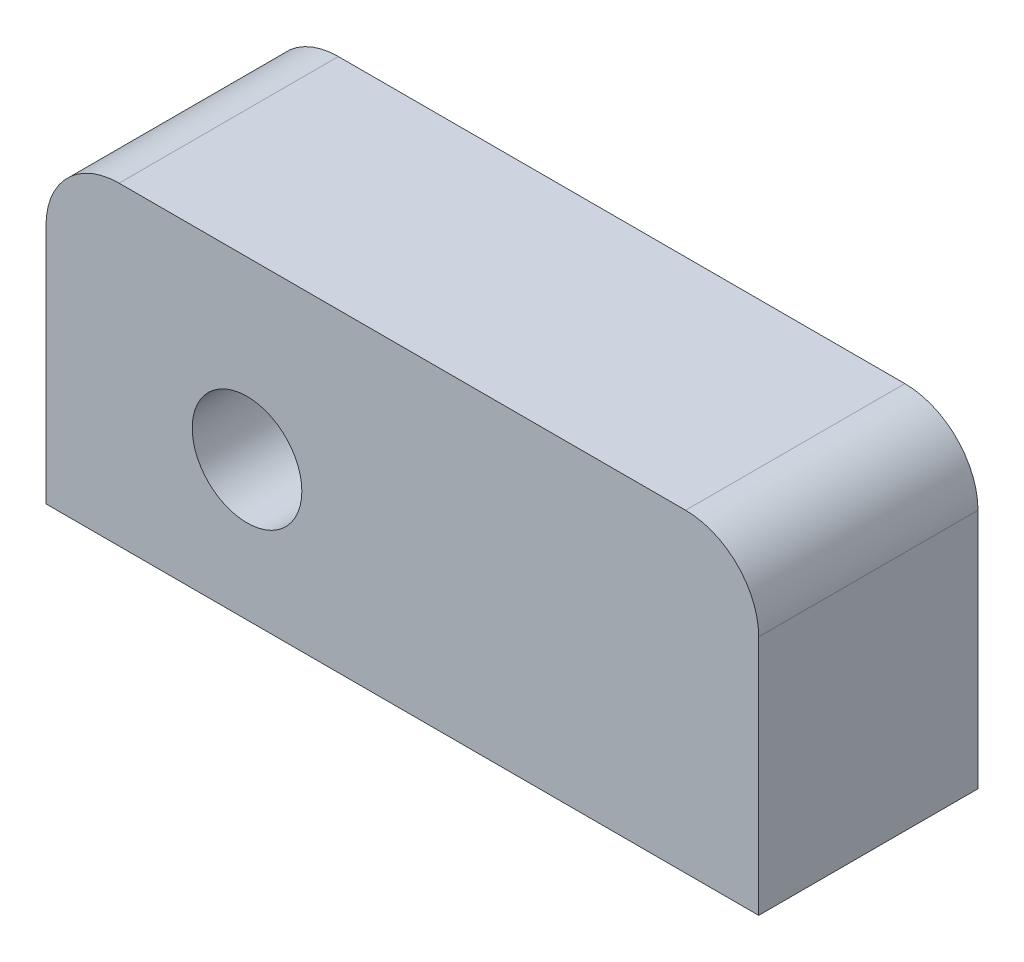
SolidWorks part; units mm, degrees
ref_plane "Płaszczyzna przednia" through (0, 0, 0) normal (0, 0, 1) x (1, 0, 0)
ref_plane "Płaszczyzna górna" through (0, 0, 0) normal (0, 1, 0) x (1, 0, 0)
ref_plane "Płaszczyzna prawa" through (0, 0, 0) normal (1, 0, 0) x (0, 0, -1)
sketch "Szkic1" plane through (0, 0, 0) normal (0, 0, 1) x (1, 0, 0)
  line L1 (-48.75, -21.5) -> (48.75, -21.5)
  line L2 (-48.75, -21.5) -> (-48.75, 21.5)
  line L3 (-48.75, 21.5) -> (48.75, 21.5)
  line L4 (48.75, -21.5) -> (48.75, 21.5)
  line L5 (-48.75, -21.5) -> (48.75, 21.5) construction
  line L6 (-48.75, 21.5) -> (48.75, -21.5) construction
  point P0 (0, 0)
  dimension "D1" = 97.5
  dimension "D2" = 43
extrude "Dodanie-wyciągnięcie1" add sketch "Szkic1" along normal blind 30
fillet "Zaokrąglenie1" radius 10 1 edges at (-48.75, 21.5, 15)
fillet "Zaokrąglenie2" radius 10 1 edges at (48.75, 21.5, 15)
sketch "Szkic2" plane through (0, 0, 30) normal (0, 0, 1) x (1, 0, 0)
  line L0 (48.75, -21.5) -> (48.75, 11.5) construction
  line L1 (38.75, 21.5) -> (-38.75, 21.5) construction
  circle A0 centre (-21.25, -2.5) radius 7.5
  dimension "D3" = 15
  dimension "D1" = 70
  dimension "D2" = 24
extrude "Wytnij-wyciągnięcie1" cut sketch "Szkic2" against normal blind 30
